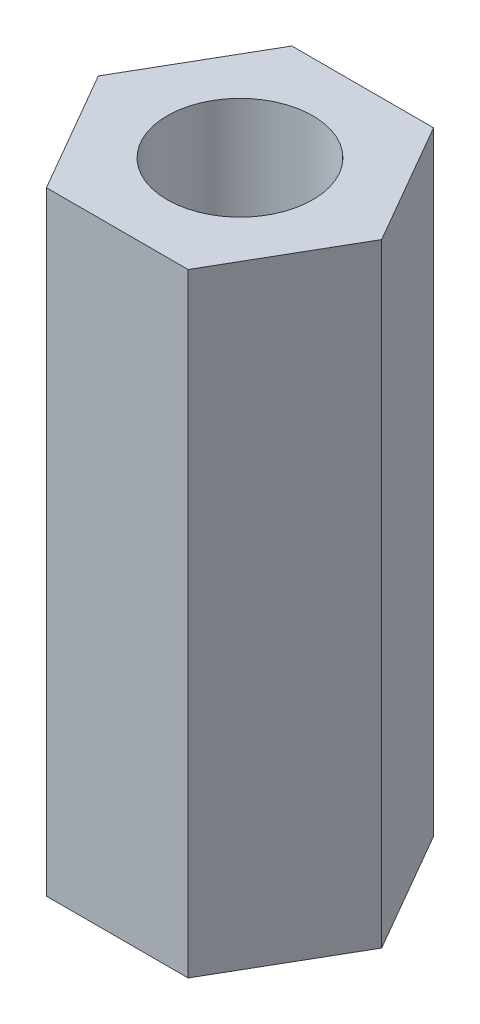
SolidWorks part; units mm, degrees
ref_plane "Front" through (0, 0, 0) normal (0, 0, 1) x (1, 0, 0)
ref_plane "Top" through (0, 0, 0) normal (0, 1, 0) x (1, 0, 0)
ref_plane "Right" through (0, 0, 0) normal (1, 0, 0) x (0, 0, -1)
sketch "Sketch1" plane through (0, 0, 0) normal (0, 1, 0) x (1, 0, 0)
  line L0 (0, 1.905) -> (0, 0) construction
  line L1 (1.0999, -1.905) -> (2.1997, 0)
  line L2 (2.1997, 0) -> (1.0999, 1.905)
  line L3 (1.0999, 1.905) -> (-1.0999, 1.905)
  line L4 (-1.0999, 1.905) -> (-2.1997, 0)
  line L5 (-2.1997, 0) -> (-1.0999, -1.905)
  line L6 (-1.0999, -1.905) -> (1.0999, -1.905)
  circle A0 centre (0, 0) radius 1.905 construction
  circle A2 centre (0, 0) radius 1.1303
  dimension "D1" = 2.2606
  dimension "D2" = 3.81
extrude "Boss-Extrude1" add sketch "Sketch1" along normal blind 9.525
